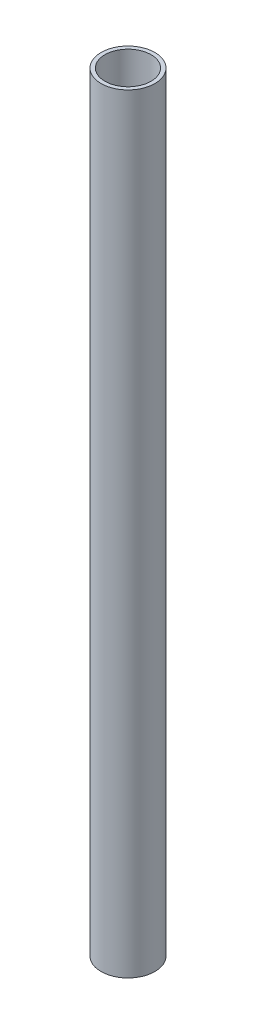
SolidWorks part; units mm, degrees
material "3.1355 (EN-AW 2024)"
ref_plane "Front" through (0, 0, 0) normal (0, 0, 1) x (1, 0, 0)
ref_plane "Top" through (0, 0, 0) normal (0, 1, 0) x (1, 0, 0)
ref_plane "Right" through (0, 0, 0) normal (1, 0, 0) x (0, 0, -1)
sketch "Эскиз1" plane through (0, 0, 0) normal (0, 1, 0) x (1, 0, 0)
  circle A0 centre (0, 0) radius 7
  circle A1 centre (0, 0) radius 6
  dimension "D1" = 14
  dimension "D2" = 12
extrude "Бобышка-Вытянуть1" add sketch "Эскиз1" along normal blind 200
